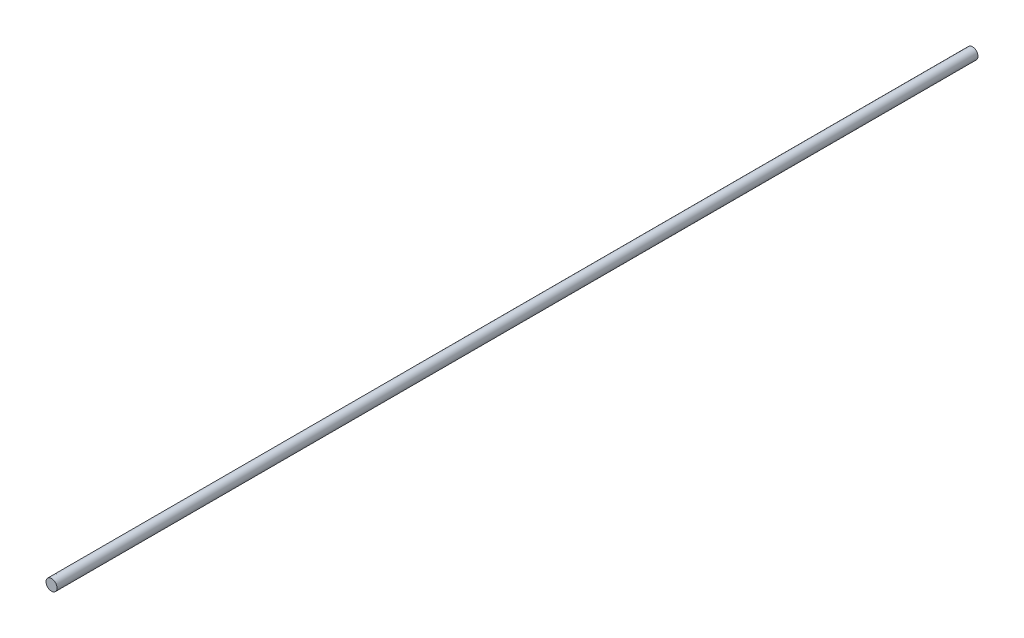
SolidWorks part; units mm, degrees
ref_plane "Front Plane" through (0, 0, 0) normal (0, 0, 1) x (1, 0, 0)
ref_plane "Top Plane" through (0, 0, 0) normal (0, 1, 0) x (1, 0, 0)
ref_plane "Right Plane" through (0, 0, 0) normal (1, 0, 0) x (0, 0, -1)
sketch "Sketch1" plane through (0, 0, 0) normal (0, 0, 1) x (1, 0, 0)
  circle A0 centre (0, 0) radius 3
  dimension "D1" = 6
extrude "Boss-Extrude1" add sketch "Sketch1" along normal mid plane 500
